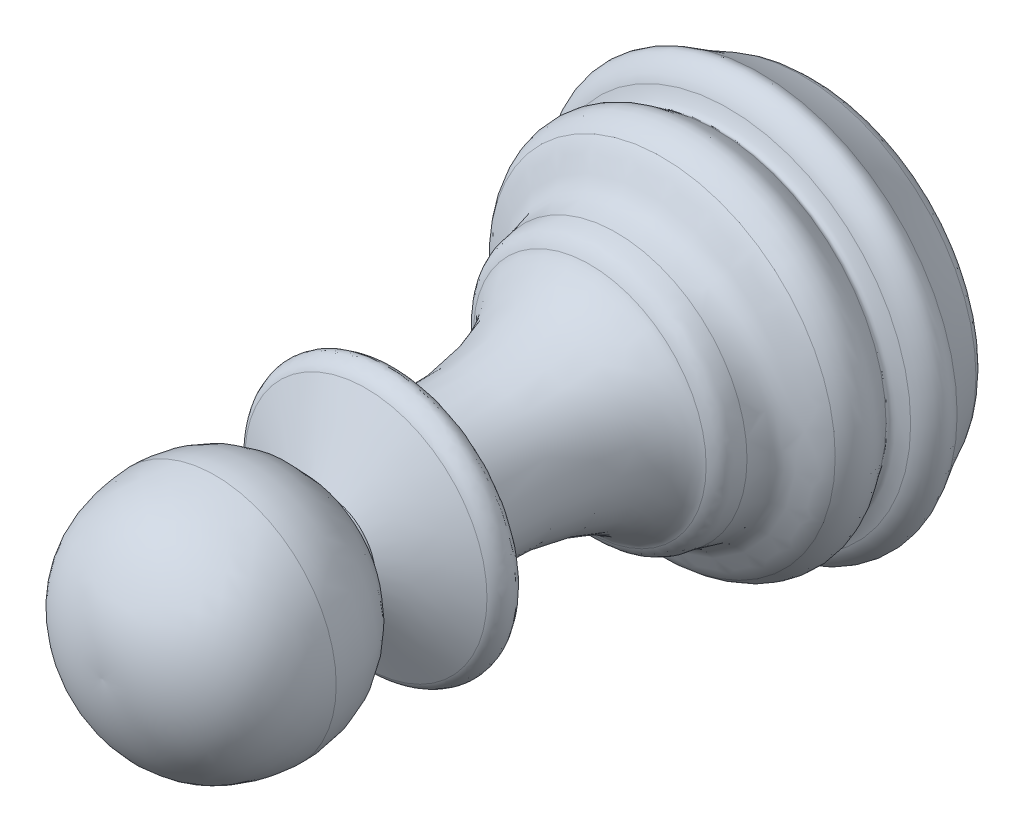
SolidWorks part; units mm, degrees
ref_plane "Front Plane" through (0, 0, 0) normal (0, 0, 1) x (1, 0, 0)
ref_plane "Top Plane" through (0, 0, 0) normal (0, 1, 0) x (1, 0, 0)
ref_plane "Right Plane" through (0, 0, 0) normal (1, 0, 0) x (0, 0, -1)
sketch "Sketch1" plane through (0, 0, 0) normal (-1, 0, 0) x (0, -1, 0)
  line L0 (0, 26.6251) -> (0, 0)
  line L1 (-6.2477, 3.8979) -> (0, 3.8979) construction
  line L2 (0, 3.8979) -> (6.2477, 3.8979) construction
  line L3 (1.749, 18.5191) -> (1.749, 18.2829)
  line L4 (1.749, 18.2829) -> (4.479, 16.8884)
  line L5 (4.1468, 15.6897) -> (2.7359, 15.6897)
  line L6 (0, 0) -> (5.5438, 0)
  spline S0 degree 3 poles (0, 26.6251) (1.262, 26.7204) (3.7808, 25.7024) (4.4106, 23.5673) (4.479, 22.4656) knots 0 0 0 0 0.578604 1 1 1 1
  spline S1 degree 2 poles (4.479, 22.4656) (4.4933, 19.7247) (1.749, 18.5191) knots 0 0 0 1 1 1
  spline S2 degree 3 poles (4.479, 16.8884) (4.6795, 16.786) (5.0672, 16.164) (4.4935, 15.6897) (4.1468, 15.6897) knots 0 0 0 0 0.447467 1 1 1 1
  spline S3 degree 3 poles (2.7359, 15.6897) (2.1364, 11.1363) (3.7161, 8.9024) (4.3019, 8.6049) knots 0 0 0 0 1 1 1 1
  spline S4 degree 3 poles (4.3019, 8.6049) (4.4597, 8.5248) (4.7787, 8.2759) (4.7999, 7.8941) (4.834, 7.6252) knots 0 0 0 0 0.408406 1 1 1 1
  spline S5 degree 3 poles (4.834, 7.6252) (4.8747, 7.3037) (5.109, 6.4492) (6.007, 6.3433) (6.4024, 5.9302) knots 0 0 0 0 0.377645 1 1 1 1
  spline S6 degree 3 poles (6.4024, 5.9302) (6.7842, 5.5313) (6.9517, 4.7282) (6.4263, 4.16) (6.2477, 3.8979) knots 0 0 0 0 0.588502 1 1 1 1
  spline S7 degree 3 poles (6.2477, 3.8979) (6.2187, 3.8553) (6.1839, 3.7178) (6.4451, 3.5733) (6.69, 3.498) (6.7414, 3.4785) knots 0 0 0 0 0.162367 0.584346 1 1 1 1
  spline S8 degree 3 poles (6.7414, 3.4785) (6.9707, 3.391) (7.4012, 3.0391) (7.5394, 2.5201) (7.0853, 2.0556) knots 0 0 0 0 0.372722 1 1 1 1
  spline S9 degree 3 poles (7.0853, 2.0556) (6.8647, 1.83) (6.6096, 1.6534) (6.3198, 1.5258) knots 0 0 0 0 1 1 1 1
  spline S10 degree 2 poles (6.3198, 1.5258) (6.8893, 0.6863) (5.5438, 0) knots 0 0 0 1 1 1
  dimension "D1" = 6.2477
  dimension "D2" = 6.2477
revolve "Revolve2" add sketch "Sketch1" angle 360 about L0
fillet "Fillet2" radius 15 1 edges at (6.3198, 0, 1.5258)
